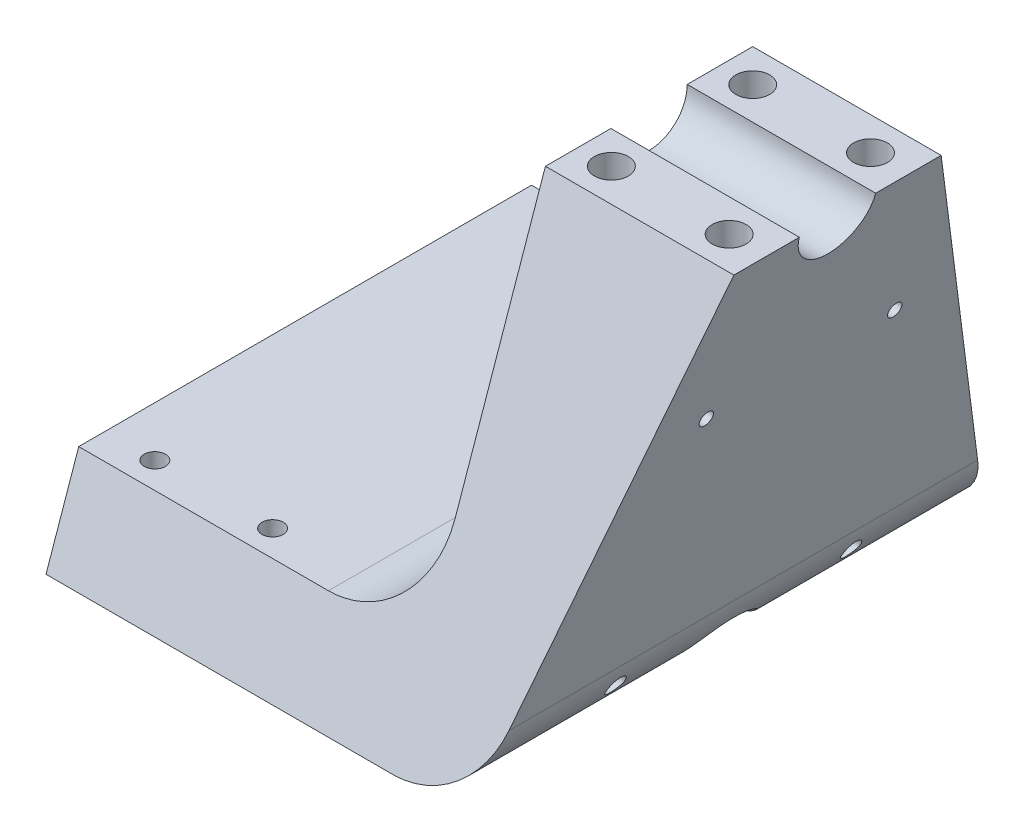
SolidWorks part; units mm, degrees
ref_plane "Front Plane" through (0, 0, 0) normal (0, 0, 1) x (1, 0, 0)
ref_plane "Top Plane" through (0, 0, 0) normal (0, 1, 0) x (1, 0, 0)
ref_plane "Right Plane" through (0, 0, 0) normal (1, 0, 0) x (0, 0, -1)
sketch "Sketch1" plane through (0, 0, 0) normal (0, 0, 1) x (1, 0, 0)
  line L1 (0, 0) -> (40, 0)
  line L2 (0, 0) -> (0, -55)
  line L4 (40, 0) -> (20, -79.8588)
  line L5 (-73, -95) -> (0.5992, -95)
  line L6 (-20, -75) -> (-73, -75)
  line L7 (-73, -75) -> (-73, -95)
  arc A0 (0.5992, -95) -> (20, -79.8588) centre (0.5992, -75) ccw
  arc A1 (0, -55) -> (-20, -75) centre (-20, -55) cw
  point P14 (0, -75)
  dimension "D6" = 20
  dimension "D1" = 40
  dimension "D2" = 75
  dimension "D3" = 20
  dimension "D4" = 73
  dimension "D5" = 20
extrude "Boss-Extrude1" add sketch "Sketch1" along normal blind 110
sketch "Sketch2" plane through (0, -4.7849, 0) normal (1, 0, 0) x (0, 0, -1)
  line L0 (-110, 4.7849) -> (0, 4.7849) construction
  circle A0 centre (-55, 4.7849) radius 8.1
  dimension "D1" = 16.2
extrude "Cut-Extrude1" cut sketch "Sketch2" along normal through all
sketch "Sketch4" plane through (0, 0, 0) normal (-1, 0, 0) x (0, 0, 1)
  line L0 (33, 0) -> (0, -95)
  line L1 (46.9, 0) -> (0, 0) construction
  line L2 (77, 0) -> (110, -95)
  line L3 (110, 0) -> (63.1, 0) construction
  line L4 (33, 0) -> (0, 0)
  line L5 (0, 0) -> (0, -95)
  line L6 (77, 0) -> (110, 0)
  line L7 (110, 0) -> (110, -95)
  line L8 (110, -95) -> (0, -95) construction
  arc A0 (46.9, 0) -> (63.1, 0) centre (55, 0) ccw construction
  point P13 (55, -8.1)
  dimension "D1" = 44
  dimension "D2" = 22
extrude "Cut-Extrude2" cut sketch "Sketch4" against normal through all and the other way through all
sketch "Sketch3" plane through (0, -75, 0) normal (0, 1, 0) x (1, 0, 0)
  line L0 (-73, -103.0526) -> (-73, -6.9474) construction
  line L1 (-73, -103.0526) -> (-73, -6.9474) construction
  circle A0 centre (-62.4, -12.5) radius 2.25
  circle A1 centre (-62.4, -97.5) radius 2.25
  circle A2 centre (-37.4, -12.5) radius 2.25
  circle A3 centre (-37.4, -97.5) radius 2.25
  point P6 (-73, -55)
  dimension "D4" = 4.5
  dimension "D1" = 85
  dimension "D2" = 42.5
  dimension "D3" = 25
  dimension "D5" = 35.6
extrude "Cut-Extrude3" cut sketch "Sketch3" against normal through all
sketch "Sketch5" plane through (0, 0, 0) normal (0, 1, 0) x (1, 0, 0)
  line L0 (0, -46.9) -> (0, -33) construction
  line L2 (0, -46.9) -> (0, -63.1) construction
  circle A0 centre (7, -40) radius 3.6
  circle A1 centre (32, -40) radius 3.6
  circle A2 centre (7, -70) radius 3.6
  circle A3 centre (32, -70) radius 3.6
  point P10 (0, -55)
  dimension "D4" = 7.2
  dimension "D1" = 30
  dimension "D2" = 25
  dimension "D3" = 15
  dimension "D5" = 7
extrude "Cut-Extrude4" cut sketch "Sketch5" against normal blind 17
sketch "Sketch6" plane through (-73, 0, 0) normal (-1, 0, 0) x (0, 0, 1)
  line L0 (110, -95) -> (0, -95) construction
  circle A0 centre (55, -95) radius 10
  circle A1 centre (30, -85) radius 2
  circle A2 centre (80, -85) radius 2
  dimension "D1" = 20
  dimension "D5" = 4
  dimension "D2" = 10
  dimension "D3" = 25
  dimension "D4" = 50
extrude "Cut-Extrude5" cut sketch "Sketch6" against normal blind 149
sketch "Sketch7" plane through (37.6392, -9.4264, 0) normal (0.97, -0.2429, 0) x (0, 0, -1)
  line L0 (-104.7404, -72.6076) -> (-5.2596, -72.6076) construction
  circle A0 centre (-75, -22.6076) radius 1.5
  circle A1 centre (-35, -22.6076) radius 1.5
  point P6 (-55, -72.6076)
  dimension "D2" = 3
  dimension "D1" = 40
  dimension "D3" = 50
  dimension "D4" = 20
extrude "Cut-Extrude6" cut sketch "Sketch7" against normal blind 43
